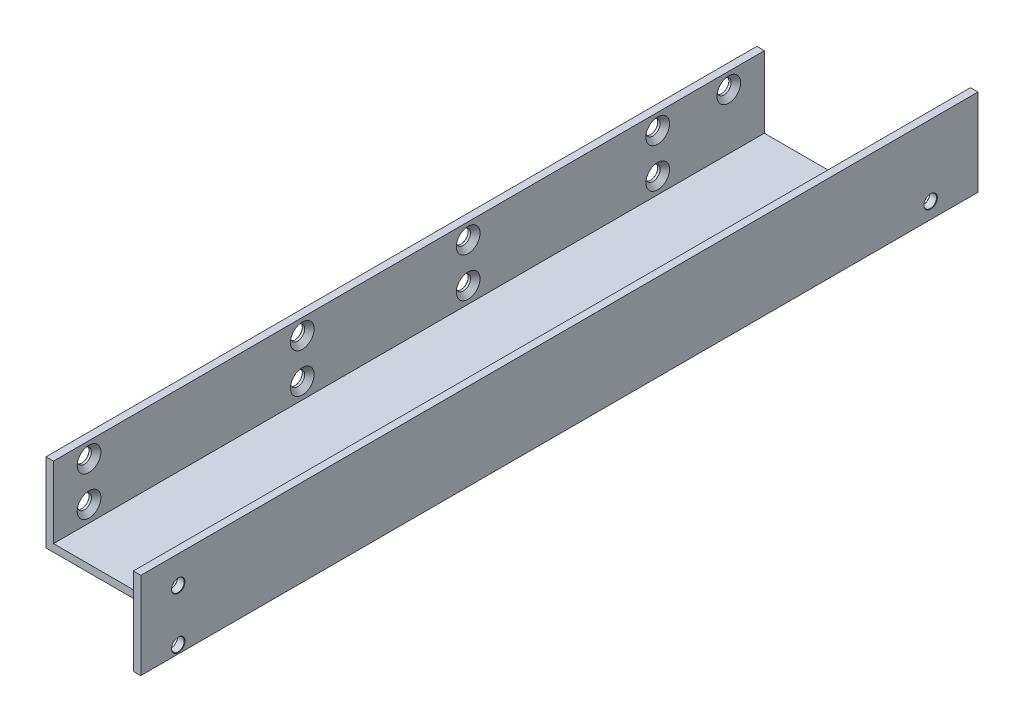
SolidWorks part; units mm, degrees
material "6063-T1"
ref_plane "Спереди" through (0, 0, 0) normal (0, 0, 1) x (1, 0, 0)
ref_plane "Сверху" through (0, 0, 0) normal (0, 1, 0) x (1, 0, 0)
ref_plane "Справа" through (0, 0, 0) normal (1, 0, 0) x (0, 0, -1)
sketch "Эскиз1" plane through (0, 0, 0) normal (0, 0, 1) x (1, 0, 0)
  line L0 (-20, 20) -> (-20, 0)
  line L1 (-20, 0) -> (20, 0)
  line L2 (20, 0) -> (20, 22)
  line L3 (-18.1, 20) -> (-18.1, 1.9)
  line L4 (-18.1, 1.9) -> (18.1, 1.9)
  line L5 (18.1, 1.9) -> (18.1, 22)
  line L6 (-20, 20) -> (-18.1, 20)
  line L7 (18.1, 22) -> (20, 22)
  dimension "D2" = 40
  dimension "D3" = 20
  dimension "D4" = 22
  dimension "D1" = 1.9
extrude "Бобышка-Вытянуть1" add sketch "Эскиз1" along normal blind 212
sketch "Эскиз2" plane through (0, 0, 0) normal (0, 1, 0) x (1, 0, 0)
  line L0 (18.1, -212) -> (18.1, -196)
  line L1 (18.1, -212) -> (18.1, 0) construction
  line L2 (18.1, -196) -> (-20, -196)
  line L3 (-20, -212) -> (-20, 0) construction
  line L4 (18.1, 0) -> (18.1, -16)
  line L5 (18.1, -16) -> (-20, -16)
  line L6 (18.1, 0) -> (-18.1, 0) construction
  line L7 (18.1, -212) -> (-18.1, -212) construction
  line M13 (-20, 0) -> (20, 0)
  line M15 (20, -212) -> (-20, -212)
  line M16 (-20, -212) -> (-20, 0)
  dimension "D1" = 16
  dimension "D2" = 16
extrude "Вырез-Вытянуть1" cut sketch "Эскиз2" along normal through all contours L2 L0 M15 M16 | L4 L5 M16 M13
sketch "Эскиз3" plane through (20, 0, 0) normal (1, 0, 0) x (0, 0, -1)
  line L0 (0, 0) -> (0, 22) construction
  line L1 (-212, 0) -> (0, 0) construction
  circle A0 centre (6, -2) radius 10
  line M1 (0, 0) -> (0, 22)
  line M4 (-212, 0) -> (0, 0)
  dimension "D1" = 20
  dimension "D2" = 6
  dimension "D3" = 2
extrude "Вырез-Вытянуть2" [suppressed] cut sketch "Эскиз3" against normal up to next contours A0 M1 M4
hole_wizard "Зенковка для винта с потайной головкой M31" positions "Эскиз5" profile "Эскиз4" countersink size "M3" standard "DIN" end condition through all
sketch "Эскиз5" plane through (-18.1, 6.7001, 54.743) normal (1, 0, 0) x (0, 0, -1)
  line L2 (-141.257, 13.2999) -> (-141.257, -6.7001) construction
  line L3 (-141.257, 13.2999) -> (38.743, 13.2999) construction
  point P1 (-36.257, -0.7001)
  point P4 (11.743, -0.7001)
  point P12 (29.743, 9.2999)
  point P15 (-78.257, -0.7001)
  point P18 (-78.257, 9.2999)
  point P21 (-132.257, 9.2999)
  point P24 (-132.257, -0.7001)
  point P26 (-36.257, 9.2999)
  point P28 (11.743, 9.2999)
  dimension "D1" = 9
  dimension "D2" = 54
  dimension "D3" = 42
  dimension "D4" = 48
  dimension "D5" = 108
  dimension "D6" = 10
  dimension "D7" = 4
sketch "Эскиз4" plane through (-18.1, 6, 91) normal (0, 1, 0) x (0, 0, -1)
  line L0 (0, 0) -> (0, 1.9)
  line L1 (0, 1.9) -> (1.9, 1.9)
  line L2 (1.8, 1.8) -> (1.8, 1.2)
  line L3 (1.8, 1.2) -> (3, 0)
  line L5 (3, 0) -> (0, 0)
  line L6 (-1.8, 1.2) -> (-3, 0) construction
  line L7 (1.9, 1.9) -> (1.8, 1.8)
  line L8 (-1.9, 1.9) -> (-1.8, 1.8) construction
  line L11 (0, -6.35) -> (0, 107.95) construction
  dimension "Диаметр сквозного отверстия" = 3.6
  dimension "Глубина сквозного отверстия" = 1.9
  dimension "Диаметр передней зенковки" = 6
  dimension "Угол передней зенковки" = 90
  dimension "Диаметр задней зенковки" = 3.8
  dimension "Угол задней зенковки" = 90
sketch "Эскиз6" plane through (20, 0, 0) normal (1, 0, 0) x (0, 0, -1)
  line L0 (0, 0) -> (0, 22) construction
  line L1 (-212, 0) -> (0, 0) construction
  arc A0 (0, 7) -> (-8, 0) centre (1.5779, -2.8747) ccw
  line M1 (0, 0) -> (0, 22)
  line M4 (-212, 0) -> (0, 0)
  dimension "D1" = 10
  dimension "D2" = 7
  dimension "D3" = 8
extrude "Вырез-Вытянуть3" [suppressed] cut sketch "Эскиз6" against normal through all contours A0 M1 M4
hole_wizard "Отверстие с зазором M31" positions "Эскиз8" profile "Эскиз7" hole size "M3" standard "DIN" end condition up to next
sketch "Эскиз8" plane through (20, 0, 0) normal (1, 0, 0) x (0, 0, -1)
  line L1 (-212, 0) -> (0, 0) construction
  point P1 (-202.5, 2)
  point P4 (-202.5, 15)
  point P7 (-12, 4)
  dimension "D1" = 2
  dimension "D2" = 13
  dimension "D3" = 4
sketch "Эскиз7" plane through (20, 2, 202.5) normal (0, 1, 0) x (0, 0, -1)
  line L0 (0, 0) -> (0, 1.9)
  line L1 (0, 1.9) -> (1.7, 1.9)
  line L2 (1.6, 1.8) -> (1.6, 0.1)
  line L3 (1.6, 0.1) -> (1.7, 0)
  line L5 (1.7, 0) -> (0, 0)
  line L6 (-1.6, 0.1) -> (-1.7, 0) construction
  line L7 (1.7, 1.9) -> (1.6, 1.8)
  line L8 (-1.7, 1.9) -> (-1.6, 1.8) construction
  line L11 (0, -6.35) -> (0, 107.95) construction
  dimension "Диаметр сквозного отверстия" = 3.2
  dimension "Глубина сквозного отверстия" = 1.9
  dimension "Диаметр передней зенковки" = 3.4
  dimension "Угол передней зенковки" = 90
  dimension "Диаметр задней зенковки" = 3.4
  dimension "Угол задней зенковки" = 90
hole_wizard "Зенковка для винта с потайной головкой M32" positions "Эскиз10" profile "Эскиз9" countersink size "M3" standard "DIN" end condition through all
sketch "Эскиз10" plane through (0, 1.9, 0) normal (0, 1, 0) x (-1, 0, 0)
  line L0 (-18.1, 196) -> (18.1, 196) construction
  line L4 (-18.1, 196) -> (-18.1, 16) construction
  point P0 (-12.2, 186)
  point P1 (-12.2, 136)
  point P4 (-12.2, 76)
  point P7 (-12.2, 26)
  dimension "D1" = 50
  dimension "D2" = 60
  dimension "D3" = 50
  dimension "D4" = 10
  dimension "D5" = 5.9
sketch "Эскиз9" plane through (12.2, 1.9, 186) normal (1, 0, 0) x (0, 0, 1)
  line L0 (0, 0) -> (0, 1.9)
  line L1 (0, 1.9) -> (1.9, 1.9)
  line L2 (1.8, 1.8) -> (1.8, 1.2)
  line L3 (1.8, 1.2) -> (3, 0)
  line L5 (3, 0) -> (0, 0)
  line L6 (-1.8, 1.2) -> (-3, 0) construction
  line L7 (1.9, 1.9) -> (1.8, 1.8)
  line L8 (-1.9, 1.9) -> (-1.8, 1.8) construction
  line L11 (0, -6.35) -> (0, 107.95) construction
  dimension "Диаметр сквозного отверстия" = 3.6
  dimension "Глубина сквозного отверстия" = 1.9
  dimension "Диаметр передней зенковки" = 6
  dimension "Угол передней зенковки" = 90
  dimension "Диаметр задней зенковки" = 3.8
  dimension "Угол задней зенковки" = 90
